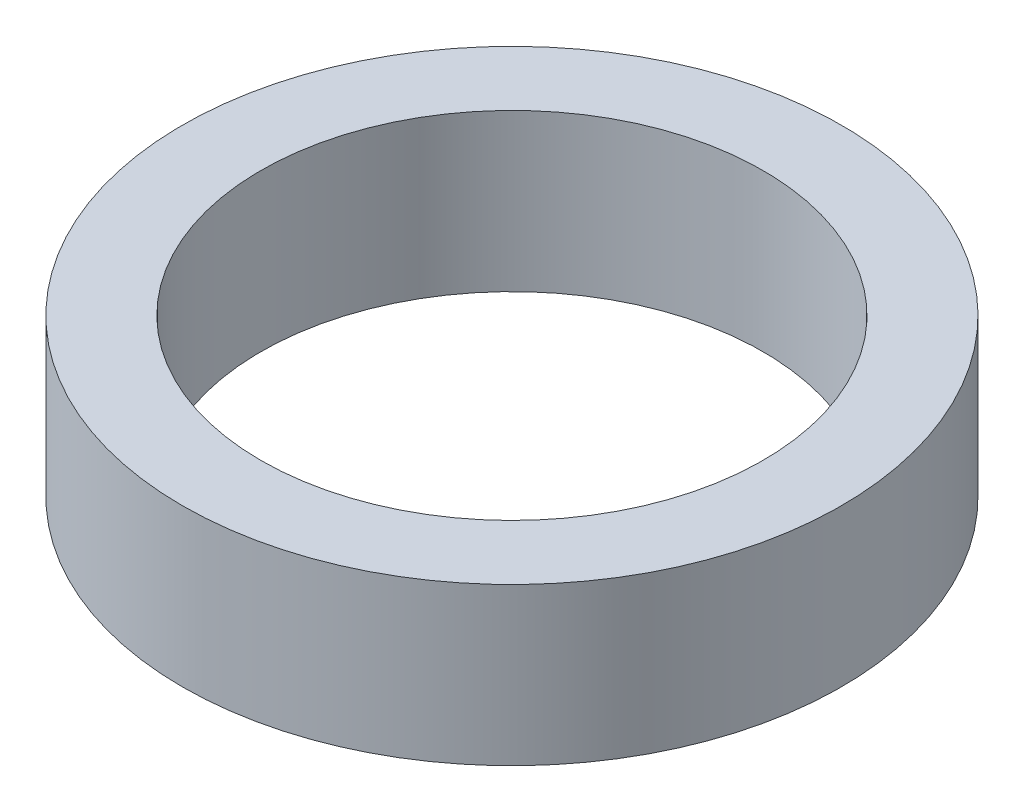
SolidWorks part; units mm, degrees
ref_plane "Front Plane" through (0, 0, 0) normal (0, 0, 1) x (1, 0, 0)
ref_plane "Top Plane" through (0, 0, 0) normal (0, 1, 0) x (1, 0, 0)
ref_plane "Right Plane" through (0, 0, 0) normal (1, 0, 0) x (0, 0, -1)
sketch "Sketch1" plane through (0, 0, 0) normal (0, 1, 0) x (1, 0, 0)
  circle A0 centre (0, 0) radius 2.1
  circle A1 centre (0, 0) radius 1.6
  dimension "D1" = 4.2
  dimension "D2" = 3.2
extrude "Boss-Extrude1" add sketch "Sketch1" along normal blind 1
